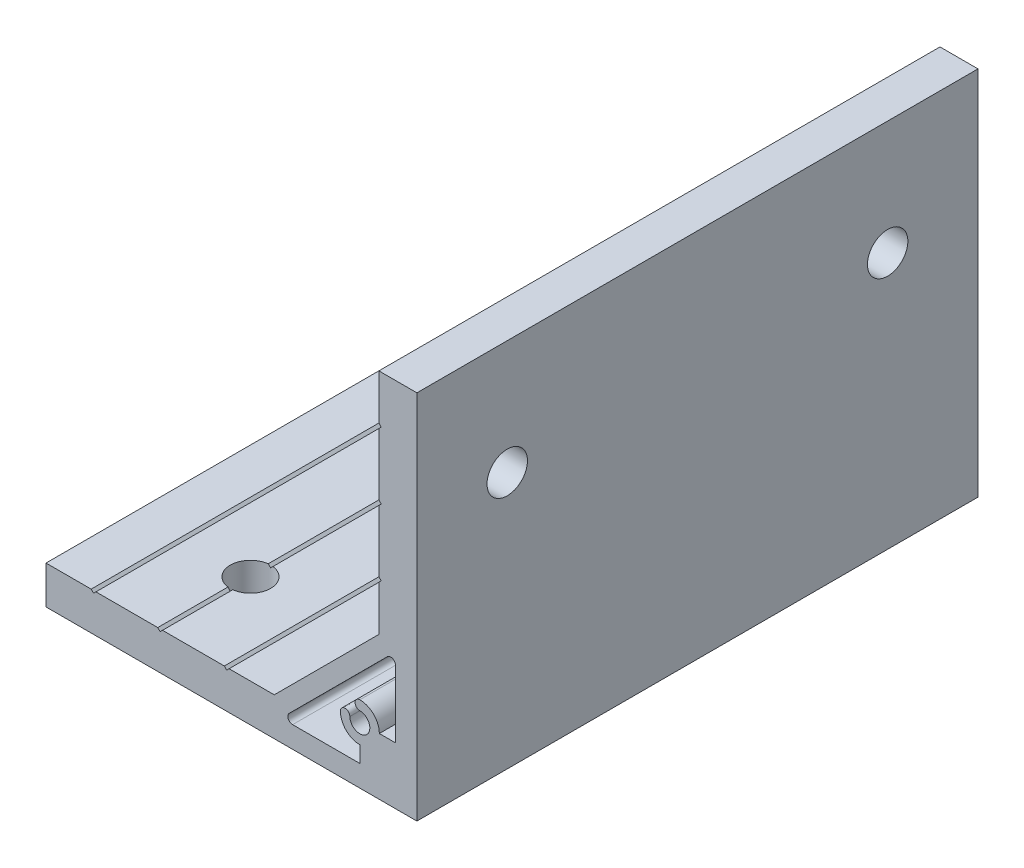
SolidWorks part; units mm, degrees
material "6063 T5"
ref_plane "Спереди" through (0, 0, 0) normal (0, 0, 1) x (1, 0, 0)
ref_plane "Сверху" through (0, 0, 0) normal (0, 1, 0) x (1, 0, 0)
ref_plane "Справа" through (0, 0, 0) normal (1, 0, 0) x (0, 0, -1)
sketch "Эскиз1" plane through (0, 0, 0) normal (0, 0, 1) x (1, 0, 0)
  line L0 (-78, 0) -> (0, 0)
  line L1 (0, 0) -> (0, 78)
  line L3 (-8, 53.5) -> (-8, 40.5)
  line L4 (-8, 40.5) -> (-7.5, 40)
  line L5 (-7.5, 40) -> (-8, 39.5)
  line L6 (-8, 39.5) -> (-8, 30)
  line L7 (-8, 30) -> (-30, 8)
  line L8 (-30, 8) -> (-39.5, 8)
  line L9 (-39.5, 8) -> (-40, 7.5)
  line L10 (-40, 7.5) -> (-40.5, 8)
  line L11 (-40.5, 8) -> (-53.5, 8)
  line L13 (-4.5, 12) -> (-4.5, 26.136)
  line L14 (-6.2071, 26.8431) -> (-26.8431, 6.2071)
  line L15 (-26.136, 4.5) -> (-12, 4.5)
  line L16 (-12, 4.5) -> (-12, 7.9)
  line L17 (-7.9, 12) -> (-4.5, 12)
  line L18 (-8, 53.5) -> (-7.5, 54)
  line L19 (-7.5, 54) -> (-8, 54.5)
  line L20 (-8, 54.5) -> (-8, 67.5)
  line L21 (-8, 67.5) -> (-7.5, 68)
  line L22 (-7.5, 68) -> (-8, 68.5)
  line L23 (-8, 68.5) -> (-8, 78)
  line L24 (-8, 78) -> (0, 78)
  line L25 (-53.5, 8) -> (-54, 7.5)
  line L26 (-54, 7.5) -> (-54.5, 8)
  line L27 (-54.5, 8) -> (-67.5, 8)
  line L28 (-67.5, 8) -> (-68, 7.5)
  line L29 (-68, 7.5) -> (-68.5, 8)
  line L30 (-68.5, 8) -> (-78, 8)
  line L31 (-78, 8) -> (-78, 0)
  arc A0 (-4.5, 26.136) -> (-6.2071, 26.8431) centre (-5.5, 26.136) ccw
  arc A1 (-26.8431, 6.2071) -> (-26.136, 4.5) centre (-26.136, 5.5) ccw
  arc A2 (-12, 7.9) -> (-16.1, 12) centre (-12, 12) cw
  arc A3 (-16.1, 12) -> (-14.1, 12) centre (-15.1, 12) cw
  arc A4 (-14.1, 12) -> (-12, 14.1) centre (-12, 12) ccw
  arc A5 (-12, 14.1) -> (-12, 16.1) centre (-12, 15.1) cw
  arc A6 (-12, 16.1) -> (-7.9, 12) centre (-12, 12) cw
  dimension "D6" = 4.2
  dimension "D7" = 1
  dimension "D9" = 1
  dimension "D2" = 8
  dimension "D3" = 135
  dimension "D4" = 12
  dimension "D5" = 12
  dimension "D8" = 30
  dimension "D10" = 3.5
  dimension "D11" = 4.5
  dimension "D12" = 40
  dimension "D13" = 1
  dimension "D14" = 54
  dimension "D15" = 68
  dimension "D16" = 78
extrude "Бобышка-Вытянуть1" add sketch "Эскиз1" along normal mid plane 118
sketch "Эскиз2" plane through (-8, 0, 0) normal (-1, 0, 0) x (0, 0, 1)
  line L1 (59, 54) -> (-59, 54) construction
  line L2 (-40, 54) -> (40, 54) construction
  circle A0 centre (-40, 54) radius 4.25
  circle A1 centre (40, 54) radius 4.25
  point P2 (0, 54)
  dimension "D1" = 8.5
  dimension "D2" = 80
extrude "Вырез-Вытянуть1" cut sketch "Эскиз2" against normal through all
sketch "Эскиз3" plane through (0, 8, 0) normal (0, 1, 0) x (1, 0, 0)
  line L1 (-54, -59) -> (-54, 59) construction
  line L2 (-54, 40) -> (-54, -40) construction
  circle A0 centre (-54, -40) radius 4.25
  circle A1 centre (-54, 40) radius 4.25
  point P2 (-54, 0)
  dimension "D1" = 8.5
  dimension "D2" = 80
extrude "Вырез-Вытянуть2" cut sketch "Эскиз3" against normal through all
